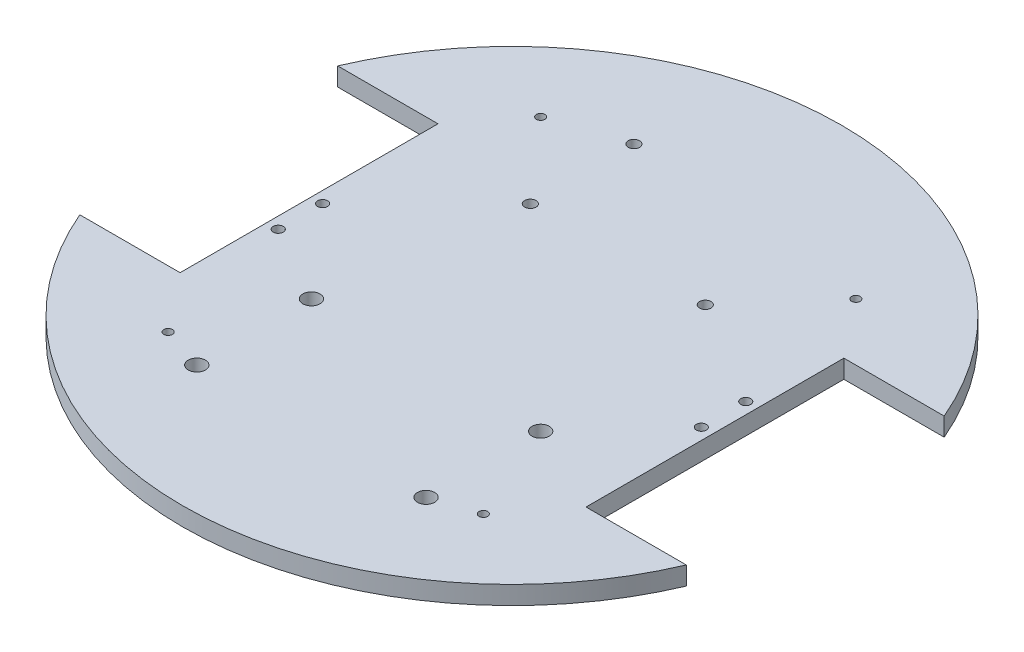
SolidWorks part; units mm, degrees
ref_plane "Front Plane" through (0, 0, 0) normal (0, 0, 1) x (1, 0, 0)
ref_plane "Top Plane" through (0, 0, 0) normal (0, 1, 0) x (1, 0, 0)
ref_plane "Right Plane" through (0, 0, 0) normal (1, 0, 0) x (0, 0, -1)
sketch "Sketch1" plane through (0, 0, 0) normal (0, 1, 0) x (1, 0, 0)
  circle A0 centre (0, 0) radius 115
  dimension "D1" = 230
extrude "Boss-Extrude1" add sketch "Sketch1" along normal blind 6.4
sketch "Sketch2" plane through (0, 6.4, 0) normal (0, 1, 0) x (1, 0, 0)
  line L0 (0, -1000) -> (0, 49000) construction
  line L1 (-105.8301, 45) -> (-70.8301, 45)
  line L2 (-70.8301, 45) -> (-70.8301, -45)
  line L3 (-70.8301, 0) -> (-115, 0)
  line L4 (-105.8301, -45) -> (-70.8301, -45)
  line L5 (105.8301, -45) -> (70.8301, -45)
  line L6 (70.8301, 0) -> (115, 0)
  line L7 (70.8301, 45) -> (70.8301, -45)
  line L8 (105.8301, 45) -> (70.8301, 45)
  circle A0 centre (0, 0) radius 115 construction
  arc A1 (-105.8301, 45) -> (-105.8301, -45) centre (0, 0) ccw
  arc A2 (105.8301, 45) -> (105.8301, -45) centre (0, 0) cw
  dimension "D1" = 45
  dimension "D2" = 35
extrude "Cut-Extrude1" cut sketch "Sketch2" against normal blind 7.5 contours L2 L4 A1 L1 | L7 L5 A2 L8
sketch "Sketch3" plane through (0, 6.4, 0) normal (0, 1, 0) x (1, 0, 0)
  line L0 (0, 0) -> (0, 50000) construction
  line L1 (0, -7) -> (-50000, -7) construction
  line L2 (-66.8301, 0) -> (-66.8301, 50000) construction
  line L3 (-70.8301, 45) -> (-70.8301, -45) construction
  line L4 (0, 0) -> (-50000, 0) construction
  circle A0 centre (-66.8301, 0.75) radius 1.75
  circle A1 centre (-66.8301, -14.75) radius 1.75
  circle A4 centre (66.8301, -0.75) radius 1.75
  circle A5 centre (66.8301, 14.75) radius 1.75
  dimension "D3" = 3.5
  dimension "D4" = 7.75
  dimension "D1" = 4
  dimension "D2" = 7
extrude "Cut-Extrude2" cut sketch "Sketch3" against normal through all
sketch "Sketch4" plane through (0, 6.4, 0) normal (0, 1, 0) x (1, 0, 0)
  line L0 (3.2139, 55) -> (50003.2139, 55) construction
  line L1 (0, 0) -> (0, 12.2932) construction
  line L2 (-33.3, 34) -> (33.3, 34) construction
  line L3 (-33.3, 34) -> (-33.3, 76) construction
  line L4 (-33.3, 76) -> (33.3, 76) construction
  line L5 (33.3, 34) -> (33.3, 76) construction
  line L6 (-33.3, 34) -> (33.3, 76) construction
  line L7 (-33.3, 76) -> (33.3, 34) construction
  circle A0 centre (30.525, 36.93) radius 1.45 construction
  circle A1 centre (30.525, 36.93) radius 2
  circle A2 centre (-30.525, 36.93) radius 2
  circle A4 centre (-30.525, 73.07) radius 2
  point P2 (0, 55)
  point P12 (31.975, 36.93)
  point P13 (30.525, 38.38)
  dimension "D6" = 2.9
  dimension "D7" = 4
  dimension "D1" = 55
  dimension "D2" = 66.6
  dimension "D3" = 42
  dimension "D4" = 2.65
  dimension "D5" = 2.93
extrude "Cut-Extrude3" cut sketch "Sketch4" against normal through all
sketch "Sketch5" plane through (0, 6.4, 0) normal (0, 1, 0) x (1, 0, 0)
  line L0 (0, -50) -> (50000, -50) construction
  line L2 (0, -200000) -> (0, 200012.2932) construction
  line L3 (-58.5, -66.1) -> (58.5, -66.1) construction
  line L4 (-58.5, -66.1) -> (-58.5, -33.9) construction
  line L5 (-58.5, -33.9) -> (58.5, -33.9) construction
  line L6 (58.5, -66.1) -> (58.5, -33.9) construction
  line L7 (-58.5, -66.1) -> (58.5, -33.9) construction
  line L8 (-58.5, -33.9) -> (58.5, -66.1) construction
  line L9 (0, -50) -> (0, 46961.2072) construction
  circle A0 centre (-40, -30) radius 3
  circle A1 centre (40, -30) radius 3
  circle A2 centre (40, -70) radius 3
  circle A3 centre (-40, -70) radius 3
  point P2 (0, -50)
  dimension "D4" = 6
  dimension "D1" = 50
  dimension "D2" = 117
  dimension "D3" = 32.2
  dimension "D5" = 40
  dimension "D6" = 20
extrude "Cut-Extrude4" cut sketch "Sketch5" against normal through all
hole_wizard "Ø3.0mm Dowel Hole1" positions "Sketch7" profile "Sketch6" hole size "Ø3.0" standard "ANSI Metric" end condition through all
sketch "Sketch7" plane through (0, 0, 0) normal (0, -1, 0) x (-1, 0, 0)
  point P0 (-55, 65)
  point P3 (55, 65)
  point P6 (55, -65)
  point P9 (-55, -65)
sketch "Sketch6" plane through (55, 0, -65) normal (1, 0, 0) x (0, 0, -1)
  line L0 (0, 0) -> (0, 6.4)
  line L1 (0, 6.4) -> (1.5, 6.4)
  line L2 (1.5, 6.4) -> (1.5, 0)
  line L5 (1.5, 0) -> (0, 0)
  line L11 (0, -6.35) -> (0, 107.95) construction
  dimension "Thru Hole Dia." = 3
  dimension "Thru Hole Depth" = 6.4
